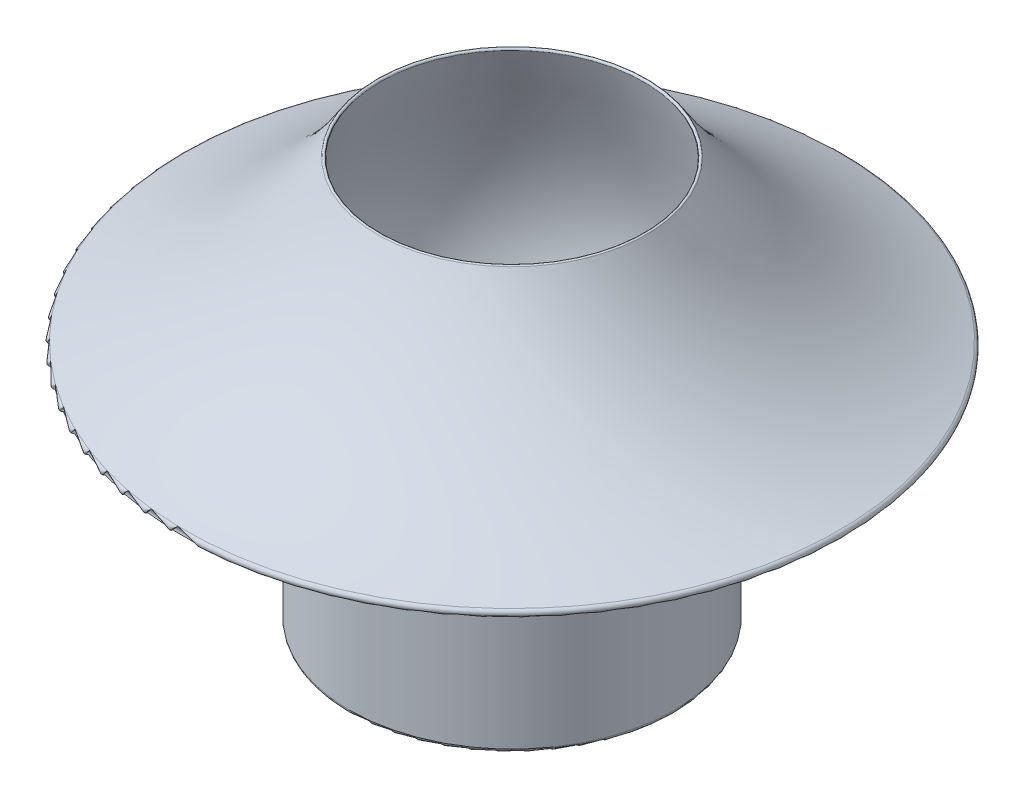
SolidWorks part; units mm, degrees
ref_plane "Front Plane" through (0, 0, 0) normal (0, 0, 1) x (1, 0, 0)
ref_plane "Top Plane" through (0, 0, 0) normal (0, 1, 0) x (1, 0, 0)
ref_plane "Right Plane" through (0, 0, 0) normal (1, 0, 0) x (0, 0, -1)
sketch "Sketch1" plane through (0, 0, 0) normal (0, 0, 1) x (1, 0, 0)
  line L0 (0, 27.2) -> (0, 0) construction
  line L2 (-9.4, 0) -> (-10.7, 0)
  line L3 (-10.7, 0) -> (-10.7, 10.6)
  line L4 (-10.7, 10.6) -> (-14.8, 10.6)
  line L5 (-14.8, 10.6) -> (-14.8, 15.5)
  line L6 (-14.8, 15.5) -> (-23, 15.5)
  arc A0 (-8.5, 27.2) -> (-23, 15.5) centre (-30.4572, 39.5768) cw
  spline S0 degree 3 poles (-8.5, 27.2) (-9.6813, 22.7311) (-12.7944, 16.5907) (-9.3827, 9.9348) (-9.3324, 5.6621) (-9.3395, 4.8466) (-9.4, 0) knots 0 0 0 0 0.480202 0.608837 0.660817 1 1 1 1
  dimension "D1" = 27.2
  dimension "D2" = 9.4
  dimension "D3" = 10.7
  dimension "D4" = 14.8
  dimension "D5" = 23
  dimension "D6" = 10.6
  dimension "D7" = 15.5
  dimension "D8" = 8.5
revolve "Revolve2" add sketch "Sketch1" angle 360 about L0
fillet "Fillet1" radius 0.1 1 edges at (-8.5, 27.2, 0)
fillet "Fillet2" radius 0.25 3 edges at (-14.8, 10.6, 0) (-10.7, 0, 0) (-23, 15.5, 0)
